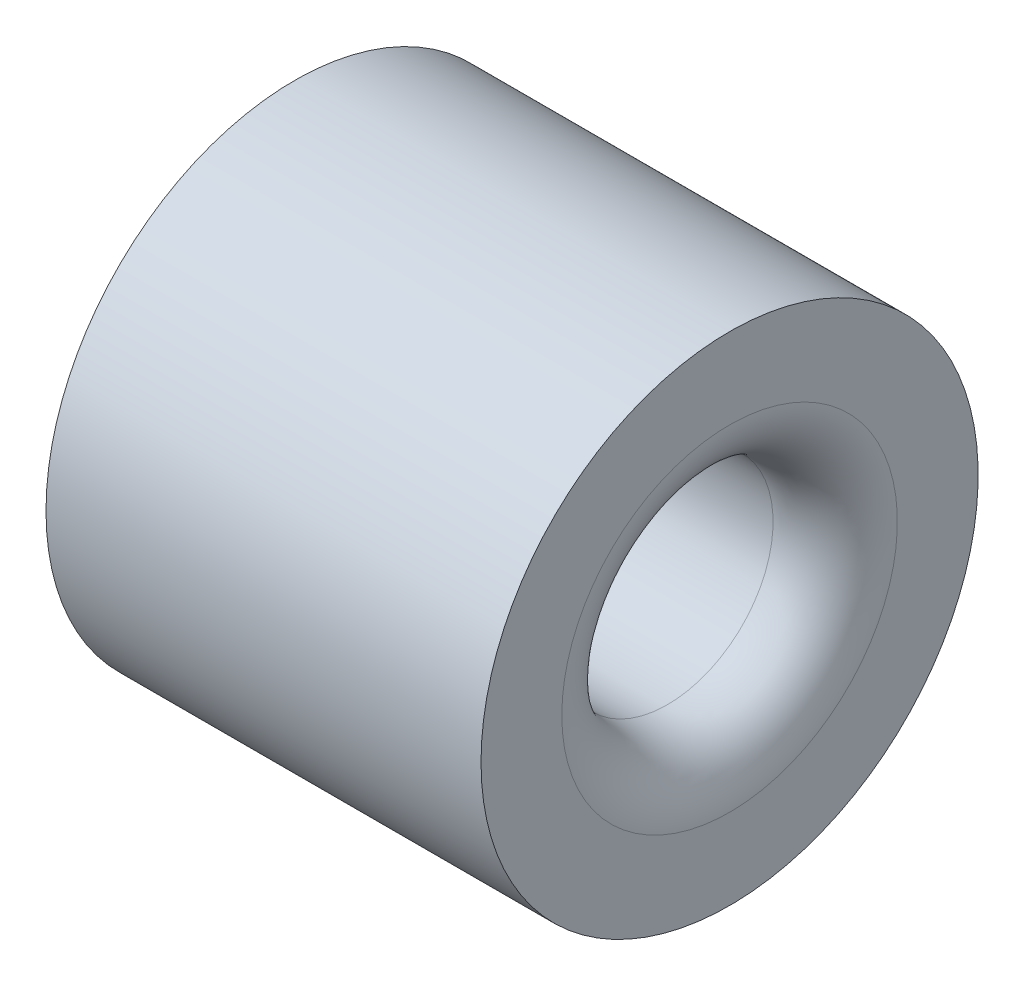
SolidWorks part; units mm, degrees
material "1.0037 (S235JR)"
ref_plane "Vorne" through (0, 0, 0) normal (0, 0, 1) x (1, 0, 0)
ref_plane "Oben" through (0, 0, 0) normal (0, 1, 0) x (1, 0, 0)
ref_plane "Rechts" through (0, 0, 0) normal (1, 0, 0) x (0, 0, -1)
sketch "Skizze1" plane through (0, 0, 0) normal (0, 0, 1) x (1, 0, 0)
  line L0 (0, 0) -> (36.1669, 0) construction
  line L2 (0, 2) -> (3.5, 2)
  line L3 (0, 2) -> (0, 0.85)
  line L4 (0, 0.85) -> (3.5, 0.85)
  line L5 (3.5, 2) -> (3.5, 0.85)
  dimension "D1" = 1.7
  dimension "D2" = 4
  dimension "D3" = 3.5
revolve "Rotation1" add sketch "Skizze1" angle 360 about L0
fillet "Verrundung1" radius 0.5 2 edges at (0, 0, 0.85) (3.5, 0, 0.85)
move or copy body "Körper-Verschieben/Kopieren1" [suppressed] bodies to move or copy 103
